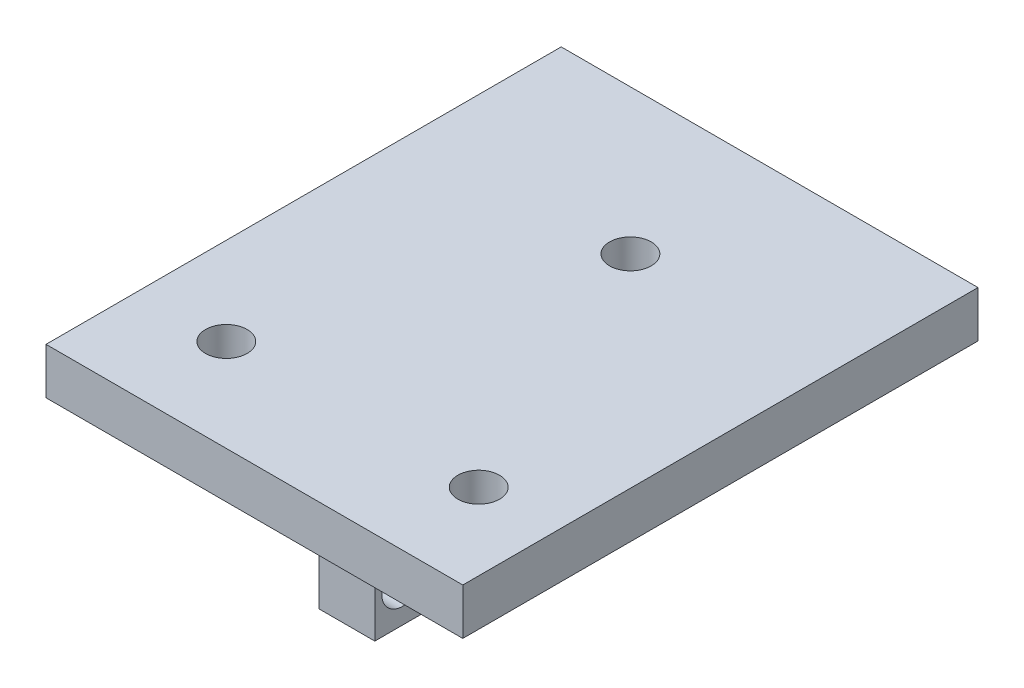
SolidWorks part; units mm, degrees
ref_plane "Front Plane" through (0, 0, 0) normal (0, 0, 1) x (1, 0, 0)
ref_plane "Top Plane" through (0, 0, 0) normal (0, 1, 0) x (1, 0, 0)
ref_plane "Right Plane" through (0, 0, 0) normal (1, 0, 0) x (0, 0, -1)
sketch "Sketch1" plane through (0, 0, 0) normal (0, 1, 0) x (1, 0, 0)
  line L0 (-14.339, 0) -> (30.661, 0)
  line L3 (8.161, 55.6215) -> (30.661, 55.6215)
  line L4 (30.661, 55.6215) -> (30.661, 0)
  line L5 (8.161, 55.6215) -> (-14.339, 55.6215)
  line L6 (-14.339, 55.6215) -> (-14.339, 0)
  dimension "D1" = 45
extrude "Boss-Extrude1" add sketch "Sketch1" along normal blind 5
hole_wizard "#8 Clearance Hole1" positions "3DSketch1" profile "Sketch2" hole size "#8" standard "ANSI Inch"
sketch3d "3DSketch1"
  line L0 (-14.339, 0, 0) -> (30.661, 0, 0) construction
  point P0 (22.3778, 0, -10)
  point P2 (-4.8722, 0, -10)
  point P4 (8.7528, 0, -40.001)
  dimension "D1" = 27.25
  dimension "D2" = 10
  dimension "D3" = 10
  dimension "D6" = 32.95
  dimension "D7" = 32.95
sketch "Sketch2" plane through (22.3778, 0, -10) normal (1, 0, 0) x (0, 0, -1)
  line L0 (0, 0) -> (0, 18.3507)
  line L1 (0, 18.3507) -> (2.2479, 17)
  line L2 (2.2479, 17) -> (2.2479, 0)
  line L5 (2.2479, 0) -> (0, 0)
  line L10 (0, 18.3507) -> (-2.2479, 17) construction
  line L11 (0, -6.35) -> (0, 107.95) construction
  dimension "Hole Dia." = 4.4958
  dimension "Hole Depth" = 17
  dimension "Drill Angle" = 118
sketch "Sketch3" plane through (0, 0, 0) normal (0, -1, 0) x (-1, 0, 0)
  line L0 (14.339, 55.6215) -> (14.339, 0) construction
  line L1 (-5.161, 50.5) -> (-11.161, 50.5)
  line L2 (-5.161, 50.5) -> (-5.161, 44.5)
  line L3 (-5.161, 44.5) -> (-11.161, 44.5)
  line L4 (-11.161, 50.5) -> (-11.161, 44.5)
  line L5 (-5.161, 16) -> (-11.161, 16)
  line L6 (-5.161, 16) -> (-5.161, 10)
  line L7 (-5.161, 10) -> (-11.161, 10)
  line L8 (-11.161, 16) -> (-11.161, 10)
  line L10 (14.339, 0) -> (-30.661, 0) construction
  dimension "D1" = 34.5
  dimension "D2" = 6
  dimension "D3" = 6
  dimension "D4" = 6
  dimension "D5" = 6
  dimension "D6" = 19.5
  dimension "D8" = 10
extrude "Boss-Extrude2" add sketch "Sketch3" along normal blind 15
hole_wizard "#8 Clearance Hole2" positions "3DSketch2" profile "Sketch16" hole size "#8" standard "ANSI Inch"
sketch3d "3DSketch2"
  line L0 (5.161, -15, -50.5) -> (5.161, 0, -50.5) construction
  line L1 (5.161, -15, -16) -> (5.161, 0, -16) construction
  line L2 (5.161, -15, -44.5) -> (5.161, -15, -50.5) construction
  line L3 (5.161, -15, -10) -> (5.161, -15, -16) construction
  point P0 (5.161, -11, -47.5)
  point P2 (5.161, -11, -13)
  dimension "D1" = 3
  dimension "D2" = 3
  dimension "D3" = 4
  dimension "D4" = 4
sketch "Sketch16" plane through (5.161, -11, -47.5) normal (0, 1, 0) x (0, 0, 1)
  line L0 (0, 0) -> (0, 18.3507)
  line L1 (0, 18.3507) -> (2.2479, 17)
  line L2 (2.2479, 17) -> (2.2479, 0)
  line L5 (2.2479, 0) -> (0, 0)
  line L10 (0, 18.3507) -> (-2.2479, 17) construction
  line L11 (0, -6.35) -> (0, 107.95) construction
  dimension "Hole Dia." = 4.4958
  dimension "Hole Depth" = 17
  dimension "Drill Angle" = 118
